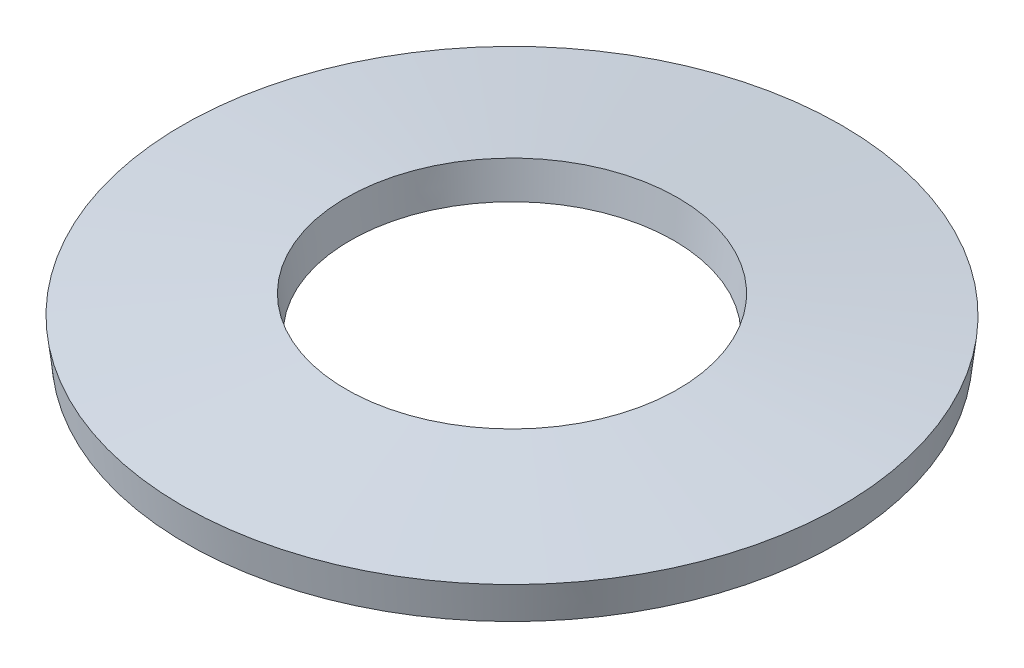
SolidWorks part; units mm, degrees
material "AISI 1045 Steel, cold drawn"
ref_plane "Front" through (0, 0, 0) normal (0, 0, 1) x (1, 0, 0)
ref_plane "Top" through (0, 0, 0) normal (0, 1, 0) x (1, 0, 0)
ref_plane "Right" through (0, 0, 0) normal (1, 0, 0) x (0, 0, -1)
sketch "Sketch1" plane through (0, 0, 0) normal (0, 0, 1) x (1, 0, 0)
  line L0 (3.5248, 0) -> (1.7526, 0.2057)
  line L1 (1.7526, 0.2057) -> (1.7965, 0.5842)
  line L2 (1.7965, 0.5842) -> (3.5687, 0.3785)
  line L3 (3.5687, 0.3785) -> (3.5248, 0)
  line L4 (0, 0) -> (0, 0.5842) construction
  dimension "ID" = 3.5052
  dimension "OD" = 7.1374
  dimension "Thickness" = 0.381
  dimension "Height" = 0.5842
revolve "Revolve1" add sketch "Sketch1" angle 360 about L4
